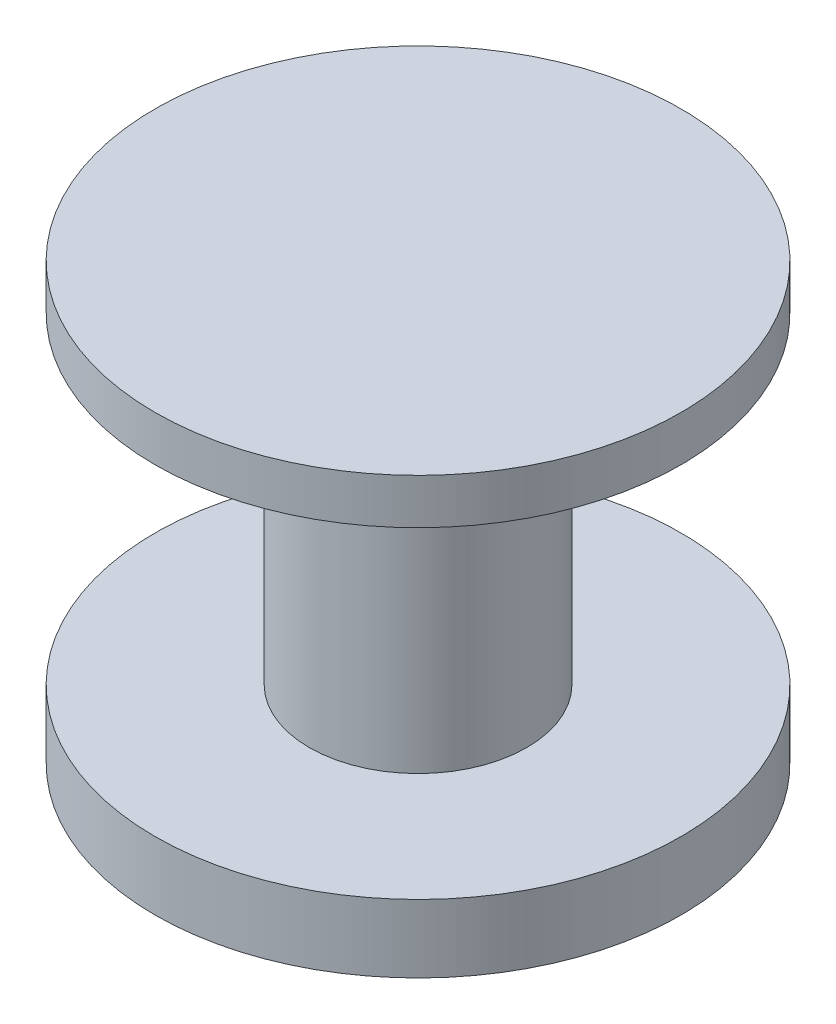
SolidWorks part; units mm, degrees
ref_plane "Front Plane" through (0, 0, 0) normal (0, 0, 1) x (1, 0, 0)
ref_plane "Top Plane" through (0, 0, 0) normal (0, 1, 0) x (1, 0, 0)
ref_plane "Right Plane" through (0, 0, 0) normal (1, 0, 0) x (0, 0, -1)
sketch "Sketch1" plane through (0, 0, 0) normal (0, 1, 0) x (1, 0, 0)
  circle A0 centre (0, 0) radius 2.9
  dimension "D1" = 5.8
extrude "Boss-Extrude1" add sketch "Sketch1" along normal blind 0.75
sketch "Sketch2" plane through (0, 0.75, 0) normal (0, 1, 0) x (1, 0, 0)
  circle A0 centre (0, 0) radius 1.2
  dimension "D1" = 2.4
extrude "Boss-Extrude2" add sketch "Sketch2" along normal blind 3.55
sketch "Sketch3" plane through (0, 4.3, 0) normal (0, 1, 0) x (1, 0, 0)
  circle A0 centre (0, 0) radius 2.9
  circle A1 centre (0, 0) radius 2.9 construction
extrude "Boss-Extrude3" add sketch "Sketch3" along normal blind 0.5
